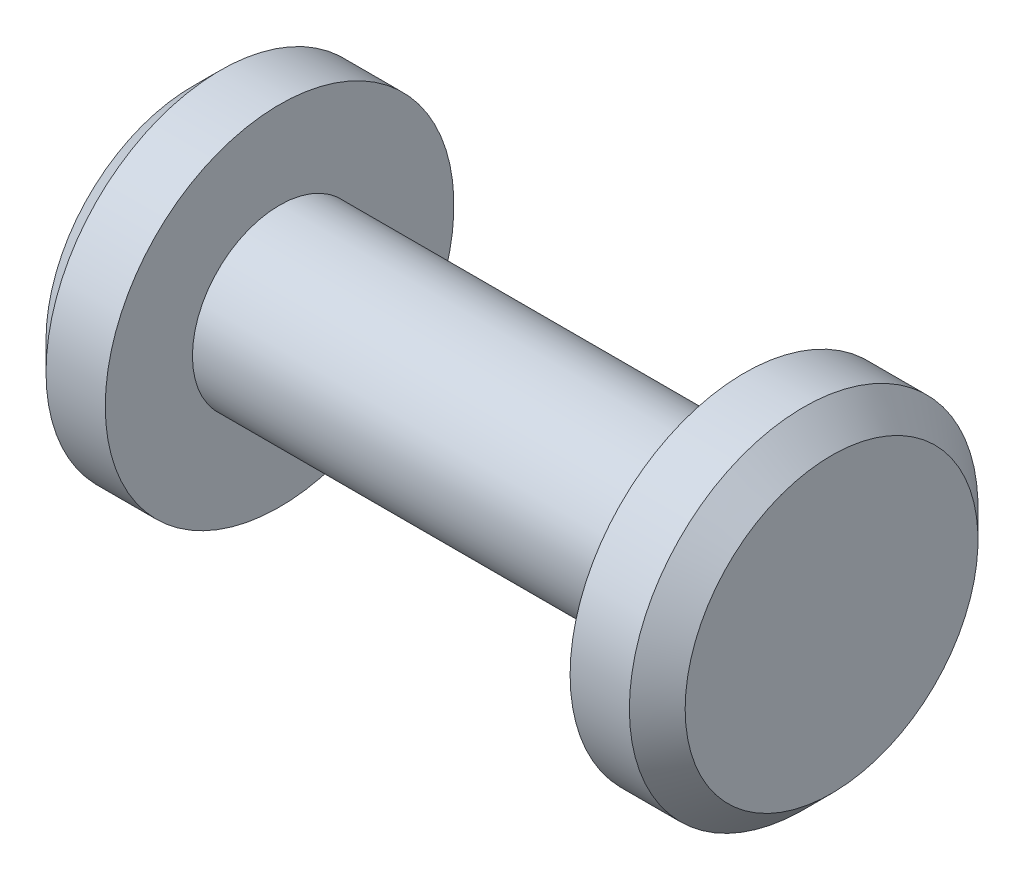
SolidWorks part; units mm, degrees
material "AISI 1015 Steel, Cold Drawn (SS)"
ref_plane "front" through (0, 0, 0) normal (0, 0, 1) x (1, 0, 0)
ref_plane "top" through (0, 0, 0) normal (0, 1, 0) x (1, 0, 0)
ref_plane "side" through (0, 0, 0) normal (1, 0, 0) x (0, 0, -1)
sketch "Sketch1" plane through (0, 0, 0) normal (0, 0, 1) x (1, 0, 0)
  line L0 (0, 0) -> (55.8636, 0) construction
  line L1 (8.7312, 0) -> (8.7312, 4.7625)
  line L2 (8.7312, 4.7625) -> (6.35, 4.7625)
  line L3 (6.35, 4.7625) -> (6.35, 2.3813)
  line L4 (6.35, 2.3813) -> (-6.35, 2.3812)
  line L5 (0, 0) -> (0, 55.2608) construction
  line L6 (-8.7312, 0) -> (8.7312, 0)
  line L7 (-6.35, 4.7625) -> (-6.35, 2.3812)
  line L8 (-8.7312, 4.7625) -> (-6.35, 4.7625)
  line L9 (-8.7312, 0) -> (-8.7312, 4.7625)
  point P12 (8.7312, -4.7625)
  point P13 (6.35, 2.3813)
  point P14 (6.35, -2.3812)
  dimension "D1" = 12.7
  dimension "D2" = 17.4625
  dimension "D3" = 4.7625
  dimension "D4" = 9.525
revolve "Base-Revolve" add sketch "Sketch1" angle 360 about L0
chamfer "Chamfer1" distance 0.762 angle 45
